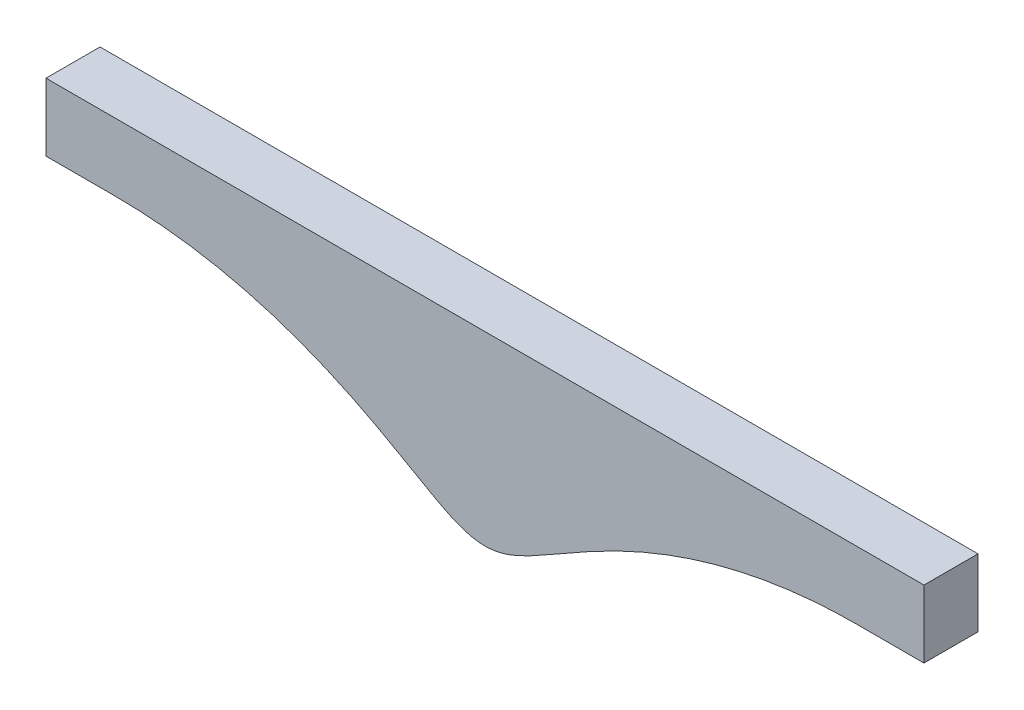
SolidWorks part; units mm, degrees
ref_plane "Front Plane" through (0, 0, 0) normal (0, 0, 1) x (1, 0, 0)
ref_plane "Top Plane" through (0, 0, 0) normal (0, 1, 0) x (1, 0, 0)
ref_plane "Right Plane" through (0, 0, 0) normal (1, 0, 0) x (0, 0, -1)
sketch "Sketch2" plane through (0, 0, 0) normal (0, 0, 1) x (1, 0, 0)
  line L17 (-69.8219, 33.3375) -> (-82.5219, 33.3375)
  line L18 (69.8219, 33.3375) -> (82.5219, 33.3375)
  line L19 (-82.5219, 33.3375) -> (-82.5219, 46.0375)
  line L20 (-82.5219, 46.0375) -> (82.5219, 46.0375)
  line L21 (82.5219, 46.0375) -> (82.5219, 33.3375)
  line L22 (0, 46.0375) -> (0, 11.1125)
  spline S0 degree 4 poles (-84.6175, 32.2371) (-84.1585, 32.3057) (-83.2397, 32.4373) (-81.399, 32.6778) (-79.322, 32.8971) (-77.472, 33.052) (-75.8511, 33.1574) (-74.9249, 33.209) (-73.9974, 33.2521) (-73.0652, 33.2865) (-72.2693, 33.3091) (-71.5691, 33.3231) (-70.9465, 33.3312) (-70.4458, 33.3355) (-69.9672, 33.3378) (-69.5639, 33.3376) (-68.9748, 33.3341) (-68.3115, 33.3268) (-67.5357, 33.3131) (-66.6499, 33.2892) (-65.5831, 33.2508) (-64.3751, 33.1921) (-63.1661, 33.1188) (-61.9583, 33.0309) (-60.7516, 32.9284) (-58.3409, 32.6942) (-55.6367, 32.3541) (-52.0475, 31.7844) (-47.5973, 30.8744) (-44.0687, 30.0037) (-40.5783, 28.9928) (-37.6983, 28.0585) (-35.4125, 27.2569) (-33.1461, 26.4021) (-30.9, 25.4954) (-28.1187, 24.2988) (-24.8241, 22.766) (-21.0443, 20.846) (-16.9885, 18.6049) (-13.1639, 16.385) (-9.6824, 14.3781) (-6.7528, 12.8394) (-4.2606, 11.8188) (-2.2896, 11.3) (-0.7275, 11.0982) (0.7275, 11.0982) (2.2896, 11.3) (4.2606, 11.8188) (6.7528, 12.8394) (9.6824, 14.3781) (13.1639, 16.385) (16.9885, 18.6049) (21.0443, 20.846) (25.3641, 23.0403) (29.2205, 24.8023) (32.5795, 26.1884) (35.4125, 27.2569) (37.6983, 28.0585) (40.5783, 28.9927) (44.0687, 30.0037) (48.1853, 31.0195) (52.3464, 31.8356) (55.9373, 32.3907) (58.9434, 32.7564) (61.3533, 32.9906) (63.4691, 33.1445) (65.2794, 33.2398) (66.6495, 33.2892) (67.5358, 33.3131) (68.3115, 33.3268) (68.9748, 33.3341) (69.5639, 33.3376) (69.9672, 33.3378) (70.557, 33.335) (71.3354, 33.3275) (72.1552, 33.3124) (73.0653, 33.2865) (73.9973, 33.2521) (74.9249, 33.209) (75.8511, 33.1574) (77.472, 33.052) (79.322, 32.8971) (81.399, 32.6778) (83.2397, 32.4373) (84.1585, 32.3057) (84.6175, 32.2371) knots 0 0 0 0 0 0.010416 0.020831 0.041663 0.046871 0.052078 0.057286 0.062494 0.067702 0.07291 0.075514 0.078118 0.080722 0.083326 0.086723 0.090121 0.093518 0.096916 0.103711 0.110506 0.117301 0.124096 0.130891 0.137686 0.144481 0.178457 0.192047 0.219227 0.246408 0.259998 0.273588 0.287178 0.300769 0.314359 0.327949 0.355129 0.38231 0.40949 0.431936 0.454382 0.472502 0.483717 0.492235 0.5 0.507765 0.516283 0.527498 0.545618 0.568064 0.59051 0.61769 0.644871 0.672051 0.699231 0.712822 0.726412 0.740002 0.753592 0.780773 0.807953 0.835133 0.848724 0.862314 0.875904 0.889494 0.896289 0.903084 0.906482 0.909879 0.913277 0.916674 0.919278 0.921882 0.92709 0.932298 0.937506 0.942714 0.947922 0.953129 0.958337 0.979169 0.989584 1 1 1 1 1 construction
  spline S1 degree 4 poles (-69.8219, 33.3375) (-69.6957, 33.3375) (-69.444, 33.3369) (-68.9748, 33.3341) (-68.3115, 33.3268) (-67.5357, 33.3131) (-66.6499, 33.2892) (-65.5831, 33.2508) (-64.3751, 33.1921) (-63.1661, 33.1188) (-61.9583, 33.0309) (-60.7516, 32.9284) (-58.3409, 32.6942) (-55.6367, 32.3541) (-52.0475, 31.7844) (-47.5973, 30.8744) (-44.0687, 30.0037) (-40.5783, 28.9928) (-37.6983, 28.0585) (-35.4125, 27.2569) (-33.1461, 26.4021) (-30.9, 25.4954) (-28.1187, 24.2988) (-24.8241, 22.766) (-21.0443, 20.846) (-16.9885, 18.6049) (-13.1639, 16.385) (-9.6824, 14.3781) (-6.7528, 12.8394) (-4.2606, 11.8188) (-2.2896, 11.3) (-0.7275, 11.0982) (0.7275, 11.0982) (2.2896, 11.3) (4.2606, 11.8188) (6.7528, 12.8394) (9.6824, 14.3781) (13.1639, 16.385) (16.9885, 18.6049) (21.0443, 20.846) (25.3641, 23.0403) (29.2205, 24.8023) (32.5795, 26.1884) (35.4125, 27.2569) (37.6983, 28.0585) (40.5783, 28.9927) (44.0687, 30.0037) (48.1853, 31.0195) (52.3464, 31.8356) (55.9373, 32.3907) (58.9434, 32.7564) (61.3533, 32.9906) (63.4691, 33.1445) (65.2794, 33.2398) (66.6495, 33.2892) (67.5358, 33.3131) (68.3115, 33.3268) (68.9748, 33.3341) (69.444, 33.3369) (69.6957, 33.3375) (69.8219, 33.3375) knots 0.083326 0.083326 0.083326 0.083326 0.083326 0.086723 0.090121 0.093518 0.096916 0.103711 0.110506 0.117301 0.124096 0.130891 0.137686 0.144481 0.178457 0.192047 0.219227 0.246408 0.259998 0.273588 0.287178 0.300769 0.314359 0.327949 0.355129 0.38231 0.40949 0.431936 0.454382 0.472502 0.483717 0.492235 0.5 0.507765 0.516283 0.527498 0.545618 0.568064 0.59051 0.61769 0.644871 0.672051 0.699231 0.712822 0.726412 0.740002 0.753592 0.780773 0.807953 0.835133 0.848724 0.862314 0.875904 0.889494 0.896289 0.903084 0.906482 0.909879 0.913277 0.916674 0.916674 0.916674 0.916674 0.916674
  spline S3 degree 4 poles (-84.6175, 32.2371) (-84.1585, 32.3057) (-83.2398, 32.4373) (-81.8591, 32.6177) (-80.0145, 32.824) (-78.3968, 32.9745) (-77.0093, 33.0821) (-75.6186, 33.1725) (-74.4645, 33.2334) (-73.2936, 33.2801) (-72.2691, 33.3091) (-71.5691, 33.3231) (-70.9465, 33.3312) (-70.4458, 33.3355) (-69.9672, 33.3378) (-69.5639, 33.3376) (-68.9748, 33.3341) (-68.3115, 33.3268) (-67.5357, 33.3131) (-66.6499, 33.2892) (-65.5831, 33.2508) (-64.3751, 33.1921) (-63.1661, 33.1188) (-61.9583, 33.0309) (-60.4499, 32.9028) (-57.4376, 32.5978) (-53.5372, 32.0592) (-48.7735, 31.1647) (-44.0687, 30.0037) (-40.5783, 28.9928) (-37.6983, 28.0585) (-35.4125, 27.2569) (-32.5795, 26.1884) (-29.7803, 25.0334) (-27.0169, 23.7954) (-23.7442, 22.2175) (-20.5142, 20.5531) (-16.9885, 18.6049) (-13.1639, 16.385) (-9.6824, 14.3781) (-6.7528, 12.8394) (-4.2606, 11.8188) (-2.2896, 11.3) (-0.7275, 11.0982) (0.7275, 11.0982) (2.2896, 11.3) (4.2606, 11.8188) (6.7528, 12.8394) (9.6824, 14.3781) (13.1639, 16.385) (16.9885, 18.6049) (21.0443, 20.846) (25.3641, 23.0403) (29.2205, 24.8023) (32.5795, 26.1884) (35.4125, 27.2569) (37.6982, 28.0585) (40.5783, 28.9927) (44.0686, 30.0037) (47.5973, 30.8744) (51.1574, 31.6024) (54.142, 32.1131) (56.5384, 32.4638) (58.9435, 32.7564) (61.3533, 32.9906) (63.4692, 33.1445) (65.2794, 33.2398) (66.6495, 33.2892) (67.5358, 33.3131) (68.3115, 33.3268) (68.9748, 33.3341) (69.5639, 33.3376) (69.9672, 33.3378) (70.557, 33.335) (71.2053, 33.3287) (71.8047, 33.3188) (72.4956, 33.3027) (73.1823, 33.2822) (73.9971, 33.2521) (74.9249, 33.209) (75.8511, 33.1574) (77.0089, 33.0821) (78.397, 32.9745) (80.0143, 32.824) (81.8592, 32.6177) (83.2397, 32.4373) (84.1585, 32.3057) (84.6175, 32.2371) knots 0 0 0 0 0 0.010416 0.020831 0.031247 0.041663 0.046871 0.052078 0.062494 0.067702 0.07291 0.075514 0.078118 0.080722 0.083326 0.086723 0.090121 0.093518 0.096916 0.103711 0.110506 0.117301 0.124096 0.130891 0.137686 0.151276 0.192047 0.219227 0.246408 0.259998 0.273588 0.287178 0.300769 0.327949 0.341539 0.355129 0.38231 0.40949 0.431936 0.454382 0.472502 0.483717 0.492235 0.5 0.507765 0.516283 0.527498 0.545618 0.568064 0.59051 0.61769 0.644871 0.672051 0.699231 0.712822 0.726412 0.740002 0.753592 0.780773 0.807953 0.821543 0.835133 0.848724 0.862314 0.875904 0.889494 0.896289 0.903084 0.906482 0.909879 0.913277 0.916674 0.919278 0.921882 0.92709 0.929694 0.932298 0.937506 0.942714 0.947922 0.953129 0.958337 0.968753 0.979169 0.989584 1 1 1 1 1 construction
  spline S4 degree 4 poles (-69.8219, 33.3375) (-69.6957, 33.3375) (-69.444, 33.3369) (-68.9748, 33.3341) (-68.3115, 33.3268) (-67.5357, 33.3131) (-66.6499, 33.2892) (-65.5831, 33.2508) (-64.3751, 33.1921) (-63.1661, 33.1188) (-61.9583, 33.0309) (-60.4499, 32.9028) (-57.4376, 32.5978) (-53.5372, 32.0592) (-48.7735, 31.1647) (-44.0687, 30.0037) (-40.5783, 28.9928) (-37.6983, 28.0585) (-35.4125, 27.2569) (-32.5795, 26.1884) (-29.7803, 25.0334) (-27.0169, 23.7954) (-23.7442, 22.2175) (-20.5142, 20.5531) (-16.9885, 18.6049) (-13.1639, 16.385) (-9.6824, 14.3781) (-6.7528, 12.8394) (-4.2606, 11.8188) (-2.2896, 11.3) (-0.7275, 11.0982) (0.7275, 11.0982) (2.2896, 11.3) (4.2606, 11.8188) (6.7528, 12.8394) (9.6824, 14.3781) (13.1639, 16.385) (16.9885, 18.6049) (21.0443, 20.846) (25.3641, 23.0403) (29.2205, 24.8023) (32.5795, 26.1884) (35.4125, 27.2569) (37.6982, 28.0585) (40.5783, 28.9927) (44.0686, 30.0037) (47.5973, 30.8744) (51.1574, 31.6024) (54.142, 32.1131) (56.5384, 32.4638) (58.9435, 32.7564) (61.3533, 32.9906) (63.4692, 33.1445) (65.2794, 33.2398) (66.6495, 33.2892) (67.5358, 33.3131) (68.3115, 33.3268) (68.9748, 33.3341) (69.444, 33.3369) (69.6957, 33.3375) (69.8219, 33.3375) knots 0.083326 0.083326 0.083326 0.083326 0.083326 0.086723 0.090121 0.093518 0.096916 0.103711 0.110506 0.117301 0.124096 0.130891 0.137686 0.151276 0.192047 0.219227 0.246408 0.259998 0.273588 0.287178 0.300769 0.327949 0.341539 0.355129 0.38231 0.40949 0.431936 0.454382 0.472502 0.483717 0.492235 0.5 0.507765 0.516283 0.527498 0.545618 0.568064 0.59051 0.61769 0.644871 0.672051 0.699231 0.712822 0.726412 0.740002 0.753592 0.780773 0.807953 0.821543 0.835133 0.848724 0.862314 0.875904 0.889494 0.896289 0.903084 0.906482 0.909879 0.913277 0.916674 0.916674 0.916674 0.916674 0.916674
  spline S5 degree 4 poles (-84.6175, 32.2371) (-84.1585, 32.3057) (-83.2398, 32.4373) (-81.8591, 32.6177) (-80.0145, 32.824) (-78.3968, 32.9745) (-77.0093, 33.0821) (-75.6186, 33.1725) (-74.4645, 33.2334) (-73.2936, 33.2801) (-72.2691, 33.3091) (-71.5691, 33.3231) (-70.9465, 33.3312) (-70.4458, 33.3355) (-69.9672, 33.3378) (-69.5639, 33.3376) (-68.9748, 33.3341) (-68.3115, 33.3268) (-67.5357, 33.3131) (-66.6499, 33.2892) (-65.5831, 33.2508) (-64.3751, 33.1921) (-63.1661, 33.1188) (-61.9583, 33.0309) (-60.4499, 32.9028) (-57.4376, 32.5978) (-53.5372, 32.0592) (-48.7735, 31.1647) (-44.0687, 30.0037) (-40.5783, 28.9928) (-37.6983, 28.0585) (-35.4125, 27.2569) (-32.5795, 26.1884) (-29.7803, 25.0334) (-27.0169, 23.7954) (-23.7442, 22.2175) (-20.5142, 20.5531) (-16.9885, 18.6049) (-13.1639, 16.385) (-9.6824, 14.3781) (-6.7528, 12.8394) (-4.2606, 11.8188) (-2.2896, 11.3) (-0.7275, 11.0982) (0.7275, 11.0982) (2.2896, 11.3) (4.2606, 11.8188) (6.7528, 12.8394) (9.6824, 14.3781) (13.1639, 16.385) (16.9885, 18.6049) (21.0443, 20.846) (25.3641, 23.0403) (29.2205, 24.8023) (32.5795, 26.1884) (35.4125, 27.2569) (37.6982, 28.0585) (40.5783, 28.9927) (44.0686, 30.0037) (47.5973, 30.8744) (51.1574, 31.6024) (54.142, 32.1131) (56.5384, 32.4638) (58.9435, 32.7564) (61.3533, 32.9906) (63.4692, 33.1445) (65.2794, 33.2398) (66.6495, 33.2892) (67.5358, 33.3131) (68.3115, 33.3268) (68.9748, 33.3341) (69.5639, 33.3376) (69.9672, 33.3378) (70.557, 33.335) (71.2053, 33.3287) (71.8047, 33.3188) (72.4956, 33.3027) (73.1823, 33.2822) (73.9971, 33.2521) (74.9249, 33.209) (75.8511, 33.1574) (77.0089, 33.0821) (78.397, 32.9745) (80.0143, 32.824) (81.8592, 32.6177) (83.2397, 32.4373) (84.1585, 32.3057) (84.6175, 32.2371) knots 0 0 0 0 0 0.010416 0.020831 0.031247 0.041663 0.046871 0.052078 0.062494 0.067702 0.07291 0.075514 0.078118 0.080722 0.083326 0.086723 0.090121 0.093518 0.096916 0.103711 0.110506 0.117301 0.124096 0.130891 0.137686 0.151276 0.192047 0.219227 0.246408 0.259998 0.273588 0.287178 0.300769 0.327949 0.341539 0.355129 0.38231 0.40949 0.431936 0.454382 0.472502 0.483717 0.492235 0.5 0.507765 0.516283 0.527498 0.545618 0.568064 0.59051 0.61769 0.644871 0.672051 0.699231 0.712822 0.726412 0.740002 0.753592 0.780773 0.807953 0.821543 0.835133 0.848724 0.862314 0.875904 0.889494 0.896289 0.903084 0.906482 0.909879 0.913277 0.916674 0.919278 0.921882 0.92709 0.929694 0.932298 0.937506 0.942714 0.947922 0.953129 0.958337 0.968753 0.979169 0.989584 1 1 1 1 1 construction
  spline S6 degree 4 poles (-69.8219, 33.3375) (-69.6957, 33.3375) (-69.444, 33.3369) (-68.9748, 33.3341) (-68.3115, 33.3268) (-67.5357, 33.3131) (-66.6499, 33.2892) (-65.5831, 33.2508) (-64.3751, 33.1921) (-63.1661, 33.1188) (-61.9583, 33.0309) (-60.4499, 32.9028) (-57.4376, 32.5978) (-53.5372, 32.0592) (-48.7735, 31.1647) (-44.0687, 30.0037) (-40.5783, 28.9928) (-37.6983, 28.0585) (-35.4125, 27.2569) (-32.5795, 26.1884) (-29.7803, 25.0334) (-27.0169, 23.7954) (-23.7442, 22.2175) (-20.5142, 20.5531) (-16.9885, 18.6049) (-13.1639, 16.385) (-9.6824, 14.3781) (-6.7528, 12.8394) (-4.2606, 11.8188) (-2.2896, 11.3) (-0.7275, 11.0982) (0.7275, 11.0982) (2.2896, 11.3) (4.2606, 11.8188) (6.7528, 12.8394) (9.6824, 14.3781) (13.1639, 16.385) (16.9885, 18.6049) (21.0443, 20.846) (25.3641, 23.0403) (29.2205, 24.8023) (32.5795, 26.1884) (35.4125, 27.2569) (37.6982, 28.0585) (40.5783, 28.9927) (44.0686, 30.0037) (47.5973, 30.8744) (51.1574, 31.6024) (54.142, 32.1131) (56.5384, 32.4638) (58.9435, 32.7564) (61.3533, 32.9906) (63.4692, 33.1445) (65.2794, 33.2398) (66.6495, 33.2892) (67.5358, 33.3131) (68.3115, 33.3268) (68.9748, 33.3341) (69.444, 33.3369) (69.6957, 33.3375) (69.8219, 33.3375) knots 0.083326 0.083326 0.083326 0.083326 0.083326 0.086723 0.090121 0.093518 0.096916 0.103711 0.110506 0.117301 0.124096 0.130891 0.137686 0.151276 0.192047 0.219227 0.246408 0.259998 0.273588 0.287178 0.300769 0.327949 0.341539 0.355129 0.38231 0.40949 0.431936 0.454382 0.472502 0.483717 0.492235 0.5 0.507765 0.516283 0.527498 0.545618 0.568064 0.59051 0.61769 0.644871 0.672051 0.699231 0.712822 0.726412 0.740002 0.753592 0.780773 0.807953 0.821543 0.835133 0.848724 0.862314 0.875904 0.889494 0.896289 0.903084 0.906482 0.909879 0.913277 0.916674 0.916674 0.916674 0.916674 0.916674
  dimension "D12" = 12.7
  dimension "D13" = 12.7
  dimension "D14" = 12.7
extrude "Boss-Extrude1" add sketch "Sketch2" along normal blind 10.16 contours L22 S1 L18 L21 L20 | L17 S1 L22 L20 L19
